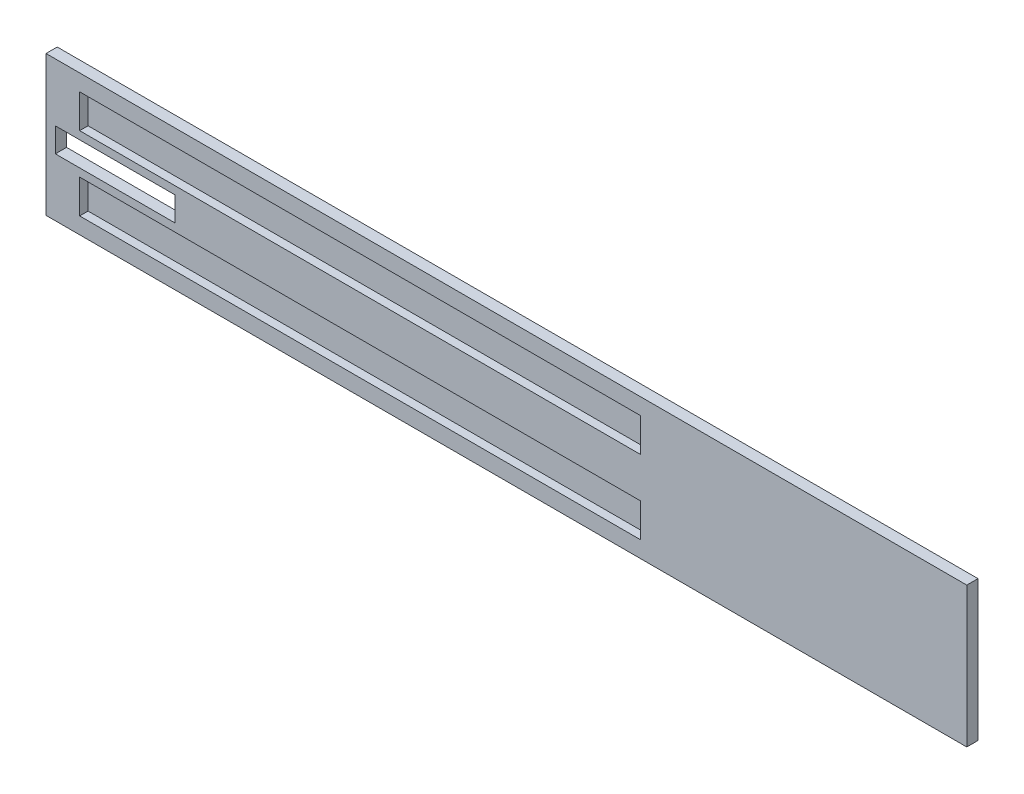
SolidWorks part; units mm, degrees
ref_plane "Alzado" through (0, 0, 0) normal (0, 0, 1) x (1, 0, 0)
ref_plane "Planta" through (0, 0, 0) normal (0, 1, 0) x (1, 0, 0)
ref_plane "Vista lateral" through (0, 0, 0) normal (1, 0, 0) x (0, 0, -1)
sketch "Croquis1" plane through (0, 0, 0) normal (0, 0, 1) x (1, 0, 0)
  line L0 (0, 0) -> (0, 150)
  line L1 (0, 150) -> (985, 150)
  line L2 (985, 150) -> (985, 0)
  line L3 (985, 0) -> (0, 0)
  dimension "D1" = 150
  dimension "D2" = 985
extrude "Saliente-Extruir1" add sketch "Croquis1" along normal blind 12
ref_plane "Plano1" through (0, 8, 0) normal (0, -1, 0) x (-1, 0, 0)
sketch "Croquis2" plane through (0, 0, 12) normal (0, 0, 1) x (1, 0, 0)
  line L0 (36, 132.5) -> (36, 17.5) construction
  line L1 (36, 96.5) -> (636, 96.5)
  line L2 (36, 75) -> (0, 75) construction
  line L3 (636, 96.5) -> (636, 132.5)
  line L4 (0, 150) -> (0, 0) construction
  line L5 (985, 150) -> (0, 150) construction
  line L6 (636, 132.5) -> (36, 132.5)
  line L7 (36, 132.5) -> (36, 96.5)
  line L8 (36, 17.5) -> (36, 53.5)
  line L9 (36, 53.5) -> (636, 53.5)
  line L10 (636, 53.5) -> (636, 17.5)
  line L11 (636, 17.5) -> (36, 17.5)
  dimension "D1" = 115
  dimension "D2" = 17.5
  dimension "D3" = 36
  dimension "D4" = 36
  dimension "D5" = 600
  dimension "D6" = 36
  dimension "D7" = 115
extrude "Cortar-Extruir1" cut sketch "Croquis2" against normal blind 9
sketch "Croquis3" plane through (0, 0, 12) normal (0, 0, 1) x (1, 0, 0)
  line L0 (10, 96.5) -> (10, 53.5) construction
  line L1 (36, 96.5) -> (636, 96.5) construction
  line L2 (636, 53.5) -> (36, 53.5) construction
  line L3 (10, 75) -> (147.2704, 75) construction
  line L4 (10, 62) -> (10, 88)
  line L5 (10, 88) -> (138.261, 88)
  line L6 (138.261, 88) -> (138.261, 62)
  line L7 (138.261, 62) -> (10, 62)
  line L8 (0, 150) -> (0, 0) construction
  point P11 (10, 75)
  dimension "D1" = 26
  dimension "D2" = 10
extrude "Cortar-Extruir2" cut sketch "Croquis3" against normal through all
